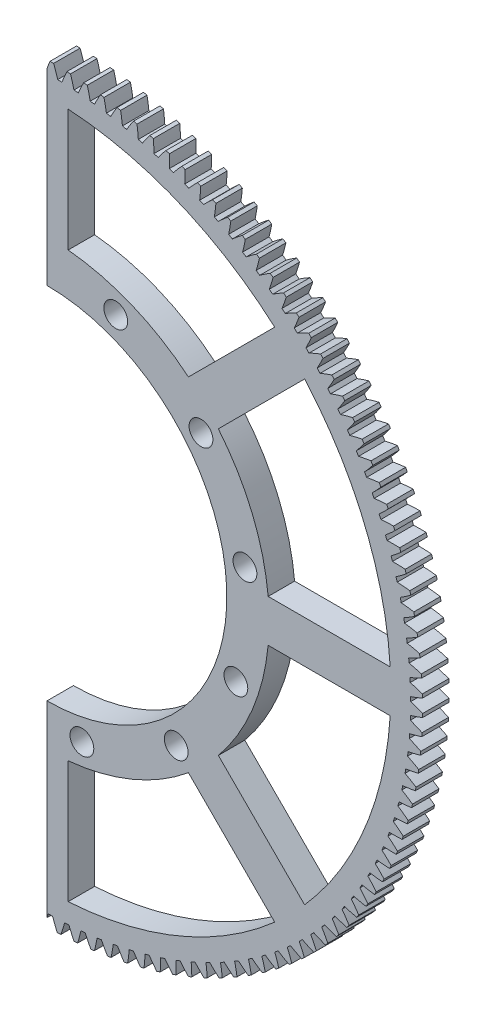
SolidWorks part; units mm, degrees
ref_plane "Front Plane" through (0, 0, 0) normal (0, 0, 1) x (1, 0, 0)
ref_plane "Top Plane" through (0, 0, 0) normal (0, 1, 0) x (1, 0, 0)
ref_plane "Right Plane" through (0, 0, 0) normal (1, 0, 0) x (0, 0, -1)
sketch "Model" plane through (0, 0, 0) normal (0, 0, 1) x (1, 0, 0)
  arc A0 (571.0314, 534.1266) -> (570.3888, 534.6291) centre (528.362, 480.2216) ccw
  arc A1 (573.0789, 535.3705) -> (571.0314, 534.1266) centre (586.5797, 510.8403) ccw
  arc A2 (573.6029, 534.9415) -> (573.0789, 535.3705) centre (528.362, 480.2216) ccw
  arc A3 (572.7875, 532.6888) -> (573.6029, 534.9415) centre (546.891, 543.3365) ccw
  arc A4 (573.4069, 532.158) -> (572.7875, 532.6888) centre (528.362, 480.2216) ccw
  arc A5 (575.5081, 533.3087) -> (573.4069, 532.158) centre (587.8948, 508.1976) ccw
  arc A6 (576.0123, 532.8566) -> (575.5081, 533.3087) centre (528.362, 480.2216) ccw
  arc A7 (575.0967, 530.6428) -> (576.0123, 532.8566) centre (549.704, 542.4416) ccw
  arc A8 (575.6916, 530.0847) -> (575.0967, 530.6428) centre (528.362, 480.2216) ccw
  arc A9 (577.8424, 531.1401) -> (575.6916, 530.0847) centre (589.09, 505.4985) ccw
  arc A10 (578.3258, 530.6658) -> (577.8424, 531.1401) centre (528.362, 480.2216) ccw
  arc A11 (577.3118, 528.4953) -> (578.3258, 530.6658) centre (552.474, 541.4215) ccw
  arc A12 (577.8811, 527.9111) -> (577.3118, 528.4953) centre (528.362, 480.2216) ccw
  arc A13 (580.077, 528.8689) -> (577.8811, 527.9111) centre (590.1629, 502.7485) ccw
  arc A14 (580.5387, 528.3734) -> (580.077, 528.8689) centre (528.362, 480.2216) ccw
  arc A15 (579.4283, 526.2505) -> (580.5387, 528.3734) centre (555.1955, 540.2781) ccw
  arc A16 (579.9708, 525.6414) -> (579.4283, 526.2505) centre (528.362, 480.2216) ccw
  arc A17 (582.2075, 526.4997) -> (579.9708, 525.6414) centre (591.1113, 499.9531) ccw
  arc A18 (582.6465, 525.984) -> (582.2075, 526.4997) centre (528.362, 480.2216) ccw
  arc A19 (581.4419, 523.9131) -> (582.6465, 525.984) centre (557.8629, 539.0137) ccw
  arc A20 (581.9566, 523.2803) -> (581.4419, 523.9131) centre (528.362, 480.2216) ccw
  arc A21 (584.2295, 524.0373) -> (581.9566, 523.2803) centre (591.9334, 497.118) ccw
  arc A22 (584.6449, 523.5025) -> (584.2295, 524.0373) centre (528.362, 480.2216) ccw
  arc A23 (583.3487, 521.4877) -> (584.6449, 523.5025) centre (560.4709, 537.631) ccw
  arc A24 (583.8344, 520.8324) -> (583.3487, 521.4877) centre (528.362, 480.2216) ccw
  arc A25 (586.1391, 521.4867) -> (583.8344, 520.8324) centre (592.6274, 494.2489) ccw
  arc A26 (586.53, 520.9338) -> (586.1391, 521.4867) centre (528.362, 480.2216) ccw
  arc A27 (585.1447, 518.9792) -> (586.53, 520.9338) centre (563.0142, 536.1326) ccw
  arc A28 (585.6006, 518.3027) -> (585.1447, 518.9792) centre (528.362, 480.2216) ccw
  arc A29 (587.9322, 518.853) -> (585.6006, 518.3027) centre (593.192, 491.3515) ccw
  arc A30 (588.298, 518.2831) -> (587.9322, 518.853) centre (528.362, 480.2216) ccw
  arc A31 (586.8264, 516.3926) -> (588.298, 518.2831) centre (565.4877, 534.5216) ccw
  arc A32 (587.2514, 515.6964) -> (586.8264, 516.3926) centre (528.362, 480.2216) ccw
  arc A33 (589.6055, 516.1415) -> (587.2514, 515.6964) centre (593.6261, 488.4317) ccw
  arc A34 (589.9453, 515.5557) -> (589.6055, 516.1415) centre (528.362, 480.2216) ccw
  arc A35 (588.3903, 513.7332) -> (589.9453, 515.5557) centre (567.8865, 532.8013) ccw
  arc A36 (588.7837, 513.0186) -> (588.3903, 513.7332) centre (528.362, 480.2216) ccw
  arc A37 (591.1553, 513.3577) -> (588.7837, 513.0186) centre (593.9287, 485.4954) ccw
  arc A38 (591.4685, 512.7572) -> (591.1553, 513.3577) centre (528.362, 480.2216) ccw
  arc A39 (589.8334, 511.0063) -> (591.4685, 512.7572) centre (570.2057, 530.9751) ccw
  arc A40 (590.1943, 510.2748) -> (589.8334, 511.0063) centre (528.362, 480.2216) ccw
  arc A41 (592.5787, 510.5071) -> (590.1943, 510.2748) centre (594.0993, 482.5484) ccw
  arc A42 (592.8647, 509.8932) -> (592.5787, 510.5071) centre (528.362, 480.2216) ccw
  arc A43 (591.1526, 508.2174) -> (592.8647, 509.8932) centre (572.4406, 529.0467) ccw
  arc A44 (591.4804, 507.4704) -> (591.1526, 508.2174) centre (528.362, 480.2216) ccw
  arc A45 (593.8728, 507.5955) -> (591.4804, 507.4704) centre (594.1375, 479.5968) ccw
  arc A46 (594.1309, 506.9694) -> (593.8728, 507.5955) centre (528.362, 480.2216) ccw
  arc A47 (592.3454, 505.3721) -> (594.1309, 506.9694) centre (574.5867, 527.0199) ccw
  arc A48 (592.6393, 504.6112) -> (592.3454, 505.3721) centre (528.362, 480.2216) ccw
  arc A49 (595.035, 504.6288) -> (592.6393, 504.6112) centre (594.0432, 476.6464) ccw
  arc A50 (595.2648, 503.9918) -> (595.035, 504.6288) centre (528.362, 480.2216) ccw
  arc A51 (593.4094, 502.4762) -> (595.2648, 503.9918) centre (576.6398, 524.899) ccw
  arc A52 (593.6688, 501.7028) -> (593.4094, 502.4762) centre (528.362, 480.2216) ccw
  arc A53 (596.0629, 501.613) -> (593.6688, 501.7028) centre (593.8167, 473.7032) ccw
  arc A54 (596.2638, 500.9662) -> (596.0629, 501.613) centre (528.362, 480.2216) ccw
  arc A55 (594.3423, 499.5354) -> (596.2638, 500.9662) centre (578.5956, 522.688) ccw
  arc A56 (594.5668, 498.7512) -> (594.3423, 499.5354) centre (528.362, 480.2216) ccw
  arc A57 (596.9544, 498.554) -> (594.5668, 498.7512) centre (593.4583, 470.7732) ccw
  arc A58 (597.1262, 497.899) -> (596.9544, 498.554) centre (528.362, 480.2216) ccw
  arc A59 (595.1424, 496.5558) -> (597.1262, 497.899) centre (580.4503, 520.3915) ccw
  arc A60 (595.3315, 495.7623) -> (595.1424, 496.5558) centre (528.362, 480.2216) ccw
  arc A61 (597.7078, 495.4582) -> (595.3315, 495.7623) centre (592.9689, 467.8621) ccw
  arc A62 (597.85, 494.7961) -> (597.7078, 495.4582) centre (528.362, 480.2216) ccw
  arc A63 (595.808, 493.5432) -> (597.85, 494.7961) centre (582.2, 518.0141) ccw
  arc A64 (595.9613, 492.7421) -> (595.808, 493.5432) centre (528.362, 480.2216) ccw
  arc A65 (598.3216, 492.3317) -> (595.9613, 492.7421) centre (592.3493, 464.976) ccw
  arc A66 (598.4339, 491.6638) -> (598.3216, 492.3317) centre (528.362, 480.2216) ccw
  arc A67 (596.3377, 490.5039) -> (598.4339, 491.6638) centre (583.8414, 515.5606) ccw
  arc A68 (596.4549, 489.6966) -> (596.3377, 490.5039) centre (528.362, 480.2216) ccw
  arc A69 (598.7945, 489.1807) -> (596.4549, 489.6966) centre (591.6009, 462.1206) ccw
  arc A70 (598.8767, 488.5085) -> (598.7945, 489.1807) centre (528.362, 480.2216) ccw
  arc A71 (596.7306, 487.4438) -> (598.8767, 488.5085) centre (585.371, 513.036) ccw
  arc A72 (596.8115, 486.6321) -> (596.7306, 487.4438) centre (528.362, 480.2216) ccw
  arc A73 (599.1255, 486.0118) -> (596.8115, 486.6321) centre (590.7251, 459.3016) ccw
  arc A74 (599.1775, 485.3366) -> (599.1255, 486.0118) centre (528.362, 480.2216) ccw
  arc A75 (596.9858, 484.3692) -> (599.1775, 485.3366) centre (586.7858, 510.4452) ccw
  arc A76 (597.0301, 483.5547) -> (596.9858, 484.3692) centre (528.362, 480.2216) ccw
  arc A77 (599.314, 482.8312) -> (597.0301, 483.5547) centre (589.7237, 456.5248) ccw
  arc A78 (599.3357, 482.1543) -> (599.314, 482.8312) centre (528.362, 480.2216) ccw
  arc A79 (597.1027, 481.2862) -> (599.3357, 482.1543) centre (588.083, 507.7936) ccw
  arc A80 (597.1105, 480.4705) -> (597.1027, 481.2862) centre (528.362, 480.2216) ccw
  arc A81 (599.3596, 479.6453) -> (597.1105, 480.4705) centre (588.5988, 453.7956) ccw
  arc A82 (599.3509, 478.9681) -> (599.3596, 479.6453) centre (528.362, 480.2216) ccw
  arc A83 (597.0813, 478.2011) -> (599.3509, 478.9681) centre (589.2598, 505.0865) ccw
  arc A84 (597.0525, 477.3859) -> (597.0813, 478.2011) centre (528.362, 480.2216) ccw
  arc A85 (599.2623, 476.4606) -> (597.0525, 477.3859) centre (587.3525, 451.1197) ccw
  arc A86 (599.2232, 475.7845) -> (599.2623, 476.4606) centre (528.362, 480.2216) ccw
  arc A87 (596.9214, 475.12) -> (599.2232, 475.7845) centre (590.3141, 502.3293) ccw
  arc A88 (596.8561, 474.307) -> (596.9214, 475.12) centre (528.362, 480.2216) ccw
  arc A89 (599.0222, 473.2834) -> (596.8561, 474.307) centre (585.9875, 448.5024) ccw
  arc A90 (598.9528, 472.6098) -> (599.0222, 473.2834) centre (528.362, 480.2216) ccw
  arc A91 (596.6235, 472.0493) -> (598.9528, 472.6098) centre (591.2435, 499.5276) ccw
  arc A92 (596.5217, 471.2399) -> (596.6235, 472.0493) centre (528.362, 480.2216) ccw
  arc A93 (598.6397, 470.1202) -> (596.5217, 471.2399) centre (584.5064, 445.949) ccw
  arc A94 (598.5402, 469.4504) -> (598.6397, 470.1202) centre (528.362, 480.2216) ccw
  arc A95 (596.1881, 468.995) -> (598.5402, 469.4504) centre (592.0464, 496.6869) ccw
  arc A96 (596.0502, 468.191) -> (596.1881, 468.995) centre (528.362, 480.2216) ccw
  arc A97 (598.1158, 466.9774) -> (596.0502, 468.191) centre (582.9122, 443.4646) ccw
  arc A98 (597.9863, 466.3127) -> (598.1158, 466.9774) centre (528.362, 480.2216) ccw
  arc A99 (595.6161, 465.9633) -> (597.9863, 466.3127) centre (592.721, 493.8132) ccw
  arc A100 (595.4422, 465.1663) -> (595.6161, 465.9633) centre (528.362, 480.2216) ccw
  arc A101 (597.4513, 463.8613) -> (595.4422, 465.1663) centre (581.2082, 441.0542) ccw
  arc A102 (597.2921, 463.203) -> (597.4513, 463.8613) centre (528.362, 480.2216) ccw
  arc A103 (594.9087, 462.9603) -> (597.2921, 463.203) centre (593.2659, 490.912) ccw
  arc A104 (594.6992, 462.1719) -> (594.9087, 462.9603) centre (528.362, 480.2216) ccw
  arc A105 (596.6478, 460.7781) -> (594.6992, 462.1719) centre (579.3977, 438.7227) ccw
  arc A106 (596.4592, 460.1276) -> (596.6478, 460.7781) centre (528.362, 480.2216) ccw
  arc A107 (594.0673, 459.992) -> (596.4592, 460.1276) centre (593.6802, 487.9894) ccw
  arc A108 (593.8226, 459.2139) -> (594.0673, 459.992) centre (528.362, 480.2216) ccw
  arc A109 (595.7067, 457.734) -> (593.8226, 459.2139) centre (577.4845, 436.4748) ccw
  arc A110 (595.4891, 457.0927) -> (595.7067, 457.734) centre (528.362, 480.2216) ccw
  arc A111 (593.0935, 457.0646) -> (595.4891, 457.0927) centre (593.9629, 485.0511) ccw
  arc A112 (592.8142, 456.2982) -> (593.0935, 457.0646) centre (528.362, 480.2216) ccw
  arc A113 (594.6299, 454.7352) -> (592.8142, 456.2982) centre (575.4724, 434.315) ccw
  arc A114 (594.3838, 454.1043) -> (594.6299, 454.7352) centre (528.362, 480.2216) ccw
  arc A115 (591.9894, 454.1837) -> (594.3838, 454.1043) centre (594.1136, 482.103) ccw
  arc A116 (591.676, 453.4306) -> (591.9894, 454.1837) centre (528.362, 480.2216) ccw
  arc A117 (593.4198, 451.7878) -> (591.676, 453.4306) centre (573.3653, 432.2476) ccw
  arc A118 (593.1456, 451.1686) -> (593.4198, 451.7878) centre (528.362, 480.2216) ccw
  arc A119 (590.7572, 451.3553) -> (593.1456, 451.1686) centre (594.1318, 479.1512) ccw
  arc A120 (590.4103, 450.617) -> (590.7572, 451.3553) centre (528.362, 480.2216) ccw
  arc A121 (592.0786, 448.8976) -> (590.4103, 450.617) centre (571.1677, 430.2769) ccw
  arc A122 (591.7769, 448.2913) -> (592.0786, 448.8976) centre (528.362, 480.2216) ccw
  arc A123 (589.3992, 448.585) -> (591.7769, 448.2913) centre (594.0175, 476.2015) ccw
  arc A124 (589.0196, 447.863) -> (589.3992, 448.585) centre (528.362, 480.2216) ccw
  arc A125 (590.6091, 446.0705) -> (589.0196, 447.863) centre (568.8838, 428.4067) ccw
  arc A126 (590.2805, 445.4784) -> (590.6091, 446.0705) centre (528.362, 480.2216) ccw
  arc A127 (587.9184, 445.8784) -> (590.2805, 445.4784) centre (593.771, 473.2599) ccw
  arc A128 (587.5067, 445.1742) -> (587.9184, 445.8784) centre (528.362, 480.2216) ccw
  arc A129 (589.0142, 443.3122) -> (587.5067, 445.1742) centre (566.5183, 426.6408) ccw
  arc A130 (588.6594, 442.7354) -> (589.0142, 443.3122) centre (528.362, 480.2216) ccw
  arc A131 (586.3176, 443.241) -> (588.6594, 442.7354) centre (593.3928, 470.3324) ccw
  arc A132 (585.8748, 442.556) -> (586.3176, 443.241) centre (528.362, 480.2216) ccw
  arc A133 (587.2972, 440.6282) -> (585.8748, 442.556) centre (564.076, 424.9829) ccw
  arc A134 (586.9169, 440.0679) -> (587.2972, 440.6282) centre (528.362, 480.2216) ccw
  arc A135 (584.6002, 440.6781) -> (586.9169, 440.0679) centre (592.8837, 467.4247) ccw
  arc A136 (584.127, 440.0136) -> (584.6002, 440.6781) centre (528.362, 480.2216) ccw
  arc A137 (585.4615, 438.024) -> (584.127, 440.0136) centre (561.5618, 423.4362) ccw
  arc A138 (585.0564, 437.4813) -> (585.4615, 438.024) centre (528.362, 480.2216) ccw
  arc A139 (582.7694, 438.1948) -> (585.0564, 437.4813) centre (592.2446, 464.5429) ccw
  arc A140 (582.2669, 437.5522) -> (582.7694, 438.1948) centre (528.362, 480.2216) ccw
  arc A141 (583.5108, 435.5047) -> (582.2669, 437.5522) centre (558.9807, 422.0039) ccw
  arc A142 (583.0818, 434.9807) -> (583.5108, 435.5047) centre (528.362, 480.2216) ccw
  arc A143 (580.8291, 435.7961) -> (583.0818, 434.9807) centre (591.4768, 461.6926) ccw
  arc A144 (580.2983, 435.1767) -> (580.8291, 435.7961) centre (528.362, 480.2216) ccw
  arc A145 (581.4491, 433.0755) -> (580.2983, 435.1767) centre (556.3379, 420.6888) ccw
  arc A146 (580.997, 432.5713) -> (581.4491, 433.0755) centre (528.362, 480.2216) ccw
  arc A147 (578.7831, 433.4869) -> (580.997, 432.5713) centre (590.582, 458.8796) ccw
  arc A148 (578.2251, 432.892) -> (578.7831, 433.4869) centre (528.362, 480.2216) ccw
  arc A149 (579.2804, 430.7412) -> (578.2251, 432.892) centre (553.6388, 419.4936) ccw
  arc A150 (578.8061, 430.2578) -> (579.2804, 430.7412) centre (528.362, 480.2216) ccw
  arc A151 (576.6356, 431.2719) -> (578.8061, 430.2578) centre (589.5618, 456.1096) ccw
  arc A152 (576.0514, 430.7025) -> (576.6356, 431.2719) centre (528.362, 480.2216) ccw
  arc A153 (577.0092, 428.5066) -> (576.0514, 430.7025) centre (550.8888, 418.4207) ccw
  arc A154 (576.5137, 428.0449) -> (577.0092, 428.5066) centre (528.362, 480.2216) ccw
  arc A155 (574.3909, 429.1554) -> (576.5137, 428.0449) centre (588.4184, 453.3882) ccw
  arc A156 (573.7817, 428.6128) -> (574.3909, 429.1554) centre (528.362, 480.2216) ccw
  arc A157 (574.64, 426.3761) -> (573.7817, 428.6128) centre (548.0934, 417.4723) ccw
  arc A158 (574.1243, 425.9372) -> (574.64, 426.3761) centre (528.362, 480.2216) ccw
  arc A159 (572.0534, 427.1417) -> (574.1243, 425.9372) centre (587.154, 450.7208) ccw
  arc A160 (571.4206, 426.627) -> (572.0534, 427.1417) centre (528.362, 480.2216) ccw
  arc A161 (572.1777, 424.3541) -> (571.4206, 426.627) centre (545.2583, 416.6503) ccw
  arc A162 (571.6428, 423.9387) -> (572.1777, 424.3541) centre (528.362, 480.2216) ccw
  arc A163 (569.628, 425.2349) -> (571.6428, 423.9387) centre (585.7713, 448.1128) ccw
  arc A164 (568.9727, 424.7492) -> (569.628, 425.2349) centre (528.362, 480.2216) ccw
  arc A165 (569.6271, 422.4446) -> (568.9727, 424.7492) centre (542.3892, 415.9562) ccw
  arc A166 (569.0741, 422.0536) -> (569.6271, 422.4446) centre (528.362, 480.2216) ccw
  arc A167 (567.1195, 423.4389) -> (569.0741, 422.0536) centre (584.2729, 445.5694) ccw
  arc A168 (566.4431, 422.9831) -> (567.1195, 423.4389) centre (528.362, 480.2216) ccw
  arc A169 (566.9934, 420.6514) -> (566.4431, 422.9831) centre (539.4918, 415.3916) ccw
  arc A170 (566.4234, 420.2856) -> (566.9934, 420.6514) centre (528.362, 480.2216) ccw
  arc A171 (564.5329, 421.7572) -> (566.4234, 420.2856) centre (582.662, 443.0959) ccw
  arc A172 (563.8367, 421.3322) -> (564.5329, 421.7572) centre (528.362, 480.2216) ccw
  arc A173 (564.2818, 418.9782) -> (563.8367, 421.3322) centre (536.572, 414.9575) ccw
  arc A174 (563.6961, 418.6383) -> (564.2818, 418.9782) centre (528.362, 480.2216) ccw
  arc A175 (561.8735, 420.1933) -> (563.6961, 418.6383) centre (580.9416, 440.6971) ccw
  arc A176 (561.1589, 419.7999) -> (561.8735, 420.1933) centre (528.362, 480.2216) ccw
  arc A177 (561.498, 417.4283) -> (561.1589, 419.7999) centre (533.6357, 414.6549) ccw
  arc A178 (560.8976, 417.1151) -> (561.498, 417.4283) centre (528.362, 480.2216) ccw
  arc A179 (559.1466, 418.7503) -> (560.8976, 417.1151) centre (579.1154, 438.3779) ccw
  arc A180 (558.4151, 418.3893) -> (559.1466, 418.7503) centre (528.362, 480.2216) ccw
  arc A181 (558.6474, 416.0049) -> (558.4151, 418.3893) centre (530.6887, 414.4843) ccw
  arc A182 (558.0335, 415.7189) -> (558.6474, 416.0049) centre (528.362, 480.2216) ccw
  arc A183 (556.3577, 417.431) -> (558.0335, 415.7189) centre (577.187, 436.143) ccw
  arc A184 (555.6107, 417.1033) -> (556.3577, 417.431) centre (528.362, 480.2216) ccw
  arc A185 (555.7359, 414.7108) -> (555.6107, 417.1033) centre (527.7371, 414.4461) ccw
  arc A186 (555.1097, 414.4527) -> (555.7359, 414.7108) centre (528.362, 480.2216) ccw
  arc A187 (553.5124, 416.2382) -> (555.1097, 414.4527) centre (575.1603, 433.9969) ccw
  arc A188 (552.7515, 415.9443) -> (553.5124, 416.2382) centre (528.362, 480.2216) ccw
  arc A189 (552.7692, 413.5486) -> (552.7515, 415.9443) centre (524.7867, 414.5404) ccw
  arc A190 (552.1321, 413.3189) -> (552.7692, 413.5486) centre (528.362, 480.2216) ccw
  arc A191 (550.6165, 415.1743) -> (552.1321, 413.3189) centre (573.0393, 431.9438) ccw
  arc A192 (549.8432, 414.9148) -> (550.6165, 415.1743) centre (528.362, 480.2216) ccw
  arc A193 (549.7533, 412.5208) -> (549.8432, 414.9148) centre (521.8435, 414.7669) ccw
  arc A194 (549.1066, 412.3198) -> (549.7533, 412.5208) centre (528.362, 480.2216) ccw
  arc A195 (547.6758, 414.2413) -> (549.1066, 412.3198) centre (570.8283, 429.988) ccw
  arc A196 (546.8915, 414.0168) -> (547.6758, 414.2413) centre (528.362, 480.2216) ccw
  arc A197 (546.6944, 411.6292) -> (546.8915, 414.0168) centre (518.9135, 415.1253) ccw
  arc A198 (546.0393, 411.4575) -> (546.6944, 411.6292) centre (528.362, 480.2216) ccw
  arc A199 (544.6961, 413.4412) -> (546.0393, 411.4575) centre (568.5318, 428.1333) ccw
  arc A200 (543.9026, 413.2521) -> (544.6961, 413.4412) centre (528.362, 480.2216) ccw
  arc A201 (543.5985, 410.8758) -> (543.9026, 413.2521) centre (516.0025, 415.6147) ccw
  arc A202 (542.9364, 410.7336) -> (543.5985, 410.8758) centre (528.362, 480.2216) ccw
  arc A203 (541.6836, 412.7757) -> (542.9364, 410.7336) centre (566.1545, 426.3836) ccw
  arc A204 (540.8824, 412.6224) -> (541.6836, 412.7757) centre (528.362, 480.2216) ccw
  arc A205 (540.472, 410.262) -> (540.8824, 412.6224) centre (513.1163, 416.2343) ccw
  arc A206 (539.8042, 410.1497) -> (540.472, 410.262) centre (528.362, 480.2216) ccw
  arc A207 (538.6442, 412.2459) -> (539.8042, 410.1497) centre (563.701, 424.7422) ccw
  arc A208 (537.837, 412.1287) -> (538.6442, 412.2459) centre (528.362, 480.2216) ccw
  arc A209 (537.3211, 409.7892) -> (537.837, 412.1287) centre (510.2609, 416.9827) ccw
  arc A210 (536.6489, 409.7069) -> (537.3211, 409.7892) centre (528.362, 480.2216) ccw
  arc A211 (535.5841, 411.853) -> (536.6489, 409.7069) centre (561.1763, 423.2126) ccw
  arc A212 (534.7724, 411.7722) -> (535.5841, 411.853) centre (528.362, 480.2216) ccw
  arc A213 (534.1521, 409.4581) -> (534.7724, 411.7722) centre (507.4419, 417.8585) ccw
  arc A214 (533.4769, 409.4061) -> (534.1521, 409.4581) centre (528.362, 480.2216) ccw
  arc A215 (532.5095, 411.5979) -> (533.4769, 409.4061) centre (558.5856, 421.7978) ccw
  arc A216 (531.695, 411.5535) -> (532.5095, 411.5979) centre (528.362, 480.2216) ccw
  arc A217 (530.9715, 409.2696) -> (531.695, 411.5535) centre (504.6651, 418.8599) ccw
  arc A218 (530.2946, 409.248) -> (530.9715, 409.2696) centre (528.362, 480.2216) ccw
  arc A219 (529.4265, 411.4809) -> (530.2946, 409.248) centre (555.934, 420.5007) ccw
  arc A220 (528.6109, 411.4731) -> (529.4265, 411.4809) centre (528.362, 480.2216) ccw
  arc A221 (527.7856, 409.224) -> (528.6109, 411.4731) centre (501.936, 419.9848) ccw
  arc A222 (527.1084, 409.2327) -> (527.7856, 409.224) centre (528.362, 480.2216) ccw
  arc A223 (526.3414, 411.5023) -> (527.1084, 409.2327) centre (553.2268, 419.3238) ccw
  arc A224 (525.5262, 411.5312) -> (526.3414, 411.5023) centre (528.362, 480.2216) ccw
  arc A225 (524.6009, 409.3213) -> (525.5262, 411.5312) centre (499.2601, 421.2311) ccw
  arc A226 (523.9248, 409.3604) -> (524.6009, 409.3213) centre (528.362, 480.2216) ccw
  arc A227 (523.2604, 411.6622) -> (523.9248, 409.3604) centre (550.4696, 418.2696) ccw
  arc A228 (522.4473, 411.7275) -> (523.2604, 411.6622) centre (528.362, 480.2216) ccw
  arc A229 (521.4238, 409.5615) -> (522.4473, 411.7275) centre (496.6428, 422.5961) ccw
  arc A230 (520.7501, 409.6309) -> (521.4238, 409.5615) centre (528.362, 480.2216) ccw
  arc A231 (520.1896, 411.9601) -> (520.7501, 409.6309) centre (547.6679, 417.3401) ccw
  arc A232 (519.3803, 412.0619) -> (520.1896, 411.9601) centre (528.362, 480.2216) ccw
  arc A233 (518.2606, 409.9439) -> (519.3803, 412.0619) centre (494.0893, 424.0772) ccw
  arc A234 (517.5907, 410.0434) -> (518.2606, 409.9439) centre (528.362, 480.2216) ccw
  arc A235 (517.1353, 412.3955) -> (517.5907, 410.0434) centre (544.8273, 416.5372) ccw
  arc A236 (516.3313, 412.5335) -> (517.1353, 412.3955) centre (528.362, 480.2216) ccw
  arc A237 (515.1178, 410.4679) -> (516.3313, 412.5335) centre (491.6049, 425.6714) ccw
  arc A238 (514.453, 410.5974) -> (515.1178, 410.4679) centre (528.362, 480.2216) ccw
  arc A239 (514.1036, 412.9675) -> (514.453, 410.5974) centre (541.9535, 415.8627) ccw
  arc A240 (513.3066, 413.1414) -> (514.1036, 412.9675) centre (528.362, 480.2216) ccw
  arc A241 (512.0016, 411.1323) -> (513.3066, 413.1414) centre (489.1946, 427.3754) ccw
  arc A242 (511.3433, 411.2915) -> (512.0016, 411.1323) centre (528.362, 480.2216) ccw
  arc A243 (511.1006, 413.6749) -> (511.3433, 411.2915) centre (539.0524, 415.3177) ccw
  arc A244 (510.3123, 413.8844) -> (511.1006, 413.6749) centre (528.362, 480.2216) ccw
  arc A245 (508.9184, 411.9359) -> (510.3123, 413.8844) centre (486.8631, 429.1859) ccw
  arc A246 (508.2679, 412.1244) -> (508.9184, 411.9359) centre (528.362, 480.2216) ccw
  arc A247 (508.1324, 414.5163) -> (508.2679, 412.1244) centre (536.1297, 414.9034) ccw
  arc A248 (507.3542, 414.761) -> (508.1324, 414.5163) centre (528.362, 480.2216) ccw
  arc A249 (505.8743, 412.877) -> (507.3542, 414.761) centre (484.6151, 431.0991) ccw
  arc A250 (505.233, 413.0945) -> (505.8743, 412.877) centre (528.362, 480.2216) ccw
  arc A251 (505.2049, 415.4901) -> (505.233, 413.0945) centre (533.1914, 414.6207) ccw
  arc A252 (504.4385, 415.7694) -> (505.2049, 415.4901) centre (528.362, 480.2216) ccw
  arc A253 (502.8756, 413.9537) -> (504.4385, 415.7694) centre (482.4553, 433.1113) ccw
  arc A254 (502.2447, 414.1998) -> (502.8756, 413.9537) centre (528.362, 480.2216) ccw
  arc A255 (502.324, 416.5942) -> (502.2447, 414.1998) centre (530.2433, 414.4701) ccw
  arc A256 (501.5709, 416.9076) -> (502.324, 416.5942) centre (528.362, 480.2216) ccw
  arc A257 (499.9281, 415.1639) -> (501.5709, 416.9076) centre (480.3879, 435.2183) ccw
  arc A258 (499.3089, 415.438) -> (499.9281, 415.1639) centre (528.362, 480.2216) ccw
  arc A259 (499.4956, 417.8265) -> (499.3089, 415.438) centre (527.2915, 414.4519) ccw
  arc A260 (498.7573, 418.1734) -> (499.4956, 417.8265) centre (528.362, 480.2216) ccw
  arc A261 (497.038, 416.505) -> (498.7573, 418.1734) centre (478.4172, 437.416) ccw
  arc A262 (496.4316, 416.8067) -> (497.038, 416.505) centre (528.362, 480.2216) ccw
  arc A263 (496.7253, 419.1844) -> (496.4316, 416.8067) centre (524.3418, 414.5661) ccw
  arc A264 (496.0034, 419.564) -> (496.7253, 419.1844) centre (528.362, 480.2216) ccw
  arc A265 (494.2109, 417.9745) -> (496.0034, 419.564) centre (476.547, 439.6998) ccw
  arc A266 (493.6187, 418.3031) -> (494.2109, 417.9745) centre (528.362, 480.2216) ccw
  arc A267 (494.0188, 420.6652) -> (493.6187, 418.3031) centre (521.4003, 414.8126) ccw
  arc A268 (493.3146, 421.0769) -> (494.0188, 420.6652) centre (528.362, 480.2216) ccw
  arc A269 (491.4526, 419.5694) -> (493.3146, 421.0769) centre (474.7812, 442.0653) ccw
  arc A270 (490.8757, 419.9242) -> (491.4526, 419.5694) centre (528.362, 480.2216) ccw
  arc A271 (491.3814, 422.266) -> (490.8757, 419.9242) centre (518.4727, 415.1908) ccw
  arc A272 (490.6963, 422.7088) -> (491.3814, 422.266) centre (528.362, 480.2216) ccw
  arc A273 (488.7686, 421.2864) -> (490.6963, 422.7088) centre (473.1233, 444.5076) ccw
  arc A274 (488.2082, 421.6667) -> (488.7686, 421.2864) centre (528.362, 480.2216) ccw
  arc A275 (488.8184, 423.9835) -> (488.2082, 421.6667) centre (515.5651, 415.7) ccw
  arc A276 (488.154, 424.4566) -> (488.8184, 423.9835) centre (528.362, 480.2216) ccw
  arc A277 (486.1643, 423.1221) -> (488.154, 424.4566) centre (471.5766, 447.0219) ccw
  arc A278 (485.6216, 423.5272) -> (486.1643, 423.1221) centre (528.362, 480.2216) ccw
  arc A279 (486.3351, 425.8142) -> (485.6216, 423.5272) centre (512.6832, 416.3391) ccw
  arc A280 (485.6925, 426.3167) -> (486.3351, 425.8142) centre (528.362, 480.2216) ccw
  arc A281 (483.645, 425.0728) -> (485.6925, 426.3167) centre (470.1442, 449.603) ccw
  arc A282 (483.121, 425.5018) -> (483.645, 425.0728) centre (528.362, 480.2216) ccw
  arc A283 (483.9365, 427.7545) -> (483.121, 425.5018) centre (509.8329, 417.1068) ccw
  arc A284 (483.3171, 428.2853) -> (483.9365, 427.7545) centre (528.362, 480.2216) ccw
  arc A285 (481.2158, 427.1345) -> (483.3171, 428.2853) centre (468.8292, 452.2457) ccw
  arc A286 (480.7116, 427.5867) -> (481.2158, 427.1345) centre (528.362, 480.2216) ccw
  arc A287 (481.6273, 429.8005) -> (480.7116, 427.5867) centre (507.0199, 418.0017) ccw
  arc A288 (481.0323, 430.3585) -> (481.6273, 429.8005) centre (528.362, 480.2216) ccw
  arc A289 (478.8816, 429.3032) -> (481.0323, 430.3585) centre (467.634, 454.9448) ccw
  arc A290 (478.3981, 429.7775) -> (478.8816, 429.3032) centre (528.362, 480.2216) ccw
  arc A291 (479.4122, 431.948) -> (478.3981, 429.7775) centre (504.2499, 419.0218) ccw
  arc A292 (478.8429, 432.5322) -> (479.4122, 431.948) centre (528.362, 480.2216) ccw
  arc A293 (476.6469, 431.5744) -> (478.8429, 432.5322) centre (466.5611, 457.6948) ccw
  arc A294 (476.1853, 432.0699) -> (476.6469, 431.5744) centre (528.362, 480.2216) ccw
  arc A295 (477.2957, 434.1927) -> (476.1853, 432.0699) centre (501.5285, 420.1652) ccw
  arc A296 (476.7532, 434.8019) -> (477.2957, 434.1927) centre (528.362, 480.2216) ccw
  arc A297 (474.5165, 433.9436) -> (476.7532, 434.8019) centre (465.6126, 460.4902) ccw
  arc A298 (474.0775, 434.4593) -> (474.5165, 433.9436) centre (528.362, 480.2216) ccw
  arc A299 (475.282, 436.5302) -> (474.0775, 434.4593) centre (498.8611, 421.4296) ccw
  arc A300 (474.7674, 437.163) -> (475.282, 436.5302) centre (528.362, 480.2216) ccw
  arc A301 (472.4944, 436.4059) -> (474.7674, 437.163) centre (464.7906, 463.3253) ccw
  arc A302 (472.079, 436.9408) -> (472.4944, 436.4059) centre (528.362, 480.2216) ccw
  arc A303 (473.3753, 438.9556) -> (472.079, 436.9408) centre (496.2531, 422.8123) ccw
  arc A304 (472.8895, 439.6109) -> (473.3753, 438.9556) centre (528.362, 480.2216) ccw
  arc A305 (470.5849, 438.9566) -> (472.8895, 439.6109) centre (464.0965, 466.1944) ccw
  arc A306 (470.1939, 439.5095) -> (470.5849, 438.9566) centre (528.362, 480.2216) ccw
  arc A307 (471.5792, 441.4641) -> (470.1939, 439.5095) centre (493.7098, 424.3107) ccw
  arc A308 (471.1234, 442.1406) -> (471.5792, 441.4641) centre (528.362, 480.2216) ccw
  arc A309 (468.7917, 441.5903) -> (471.1234, 442.1406) centre (463.5319, 469.0918) ccw
  arc A310 (468.4259, 442.1602) -> (468.7917, 441.5903) centre (528.362, 480.2216) ccw
  arc A311 (469.8976, 444.0507) -> (468.4259, 442.1602) centre (491.2362, 425.9217) ccw
  arc A312 (469.4725, 444.7469) -> (469.8976, 444.0507) centre (528.362, 480.2216) ccw
  arc A313 (467.1185, 444.3018) -> (469.4725, 444.7469) centre (463.0979, 472.0116) ccw
  arc A314 (466.7787, 444.8876) -> (467.1185, 444.3018) centre (528.362, 480.2216) ccw
  arc A315 (468.3336, 446.7101) -> (466.7787, 444.8876) centre (488.8375, 427.642) ccw
  arc A316 (467.9403, 447.4247) -> (468.3336, 446.7101) centre (528.362, 480.2216) ccw
  arc A317 (465.5686, 447.0856) -> (467.9403, 447.4247) centre (462.7952, 474.9479) ccw
  arc A318 (465.2554, 447.6861) -> (465.5686, 447.0856) centre (528.362, 480.2216) ccw
  arc A319 (466.8906, 449.437) -> (465.2554, 447.6861) centre (486.5183, 429.4682) ccw
  arc A320 (466.5297, 450.1685) -> (466.8906, 449.437) centre (528.362, 480.2216) ccw
  arc A321 (464.1452, 449.9362) -> (466.5297, 450.1685) centre (462.6247, 477.8949) ccw
  arc A322 (463.8593, 450.5501) -> (464.1452, 449.9362) centre (528.362, 480.2216) ccw
  arc A323 (465.5713, 452.2259) -> (463.8593, 450.5501) centre (484.2834, 431.3966) ccw
  arc A324 (465.2436, 452.9729) -> (465.5713, 452.2259) centre (528.362, 480.2216) ccw
  arc A325 (462.8511, 452.8478) -> (465.2436, 452.9729) centre (462.5865, 480.8465) ccw
  arc A326 (462.593, 453.4739) -> (462.8511, 452.8478) centre (528.362, 480.2216) ccw
  arc A327 (464.3785, 455.0712) -> (462.593, 453.4739) centre (482.1372, 433.4233) ccw
  arc A328 (464.0846, 455.8321) -> (464.3785, 455.0712) centre (528.362, 480.2216) ccw
  arc A329 (461.689, 455.8145) -> (464.0846, 455.8321) centre (462.6807, 483.7969) ccw
  arc A330 (461.4592, 456.4515) -> (461.689, 455.8145) centre (528.362, 480.2216) ccw
  arc A331 (463.3146, 457.9671) -> (461.4592, 456.4515) centre (480.0842, 435.5443) ccw
  arc A332 (463.0551, 458.7405) -> (463.3146, 457.9671) centre (528.362, 480.2216) ccw
  arc A333 (460.6611, 458.8303) -> (463.0551, 458.7405) centre (462.9073, 486.7401) ccw
  arc A334 (460.4601, 459.477) -> (460.6611, 458.8303) centre (528.362, 480.2216) ccw
  arc A335 (462.3817, 460.9079) -> (460.4601, 459.477) centre (478.1283, 437.7553) ccw
  arc A336 (462.1571, 461.6921) -> (462.3817, 460.9079) centre (528.362, 480.2216) ccw
  arc A337 (459.7695, 461.8892) -> (462.1571, 461.6921) centre (463.2656, 489.6701) ccw
  arc A338 (459.5978, 462.5443) -> (459.7695, 461.8892) centre (528.362, 480.2216) ccw
  arc A339 (461.5816, 463.8875) -> (459.5978, 462.5443) centre (476.2737, 440.0518) ccw
  arc A340 (461.3925, 464.681) -> (461.5816, 463.8875) centre (528.362, 480.2216) ccw
  arc A341 (459.0161, 464.9851) -> (461.3925, 464.681) centre (463.7551, 492.5812) ccw
  arc A342 (458.8739, 465.6472) -> (459.0161, 464.9851) centre (528.362, 480.2216) ccw
  arc A343 (460.916, 466.9001) -> (458.8739, 465.6472) centre (474.5239, 442.4292) ccw
  arc A344 (460.7627, 467.7012) -> (460.916, 466.9001) centre (528.362, 480.2216) ccw
  arc A345 (458.4024, 468.1116) -> (460.7627, 467.7012) centre (464.3746, 495.4673) ccw
  arc A346 (458.29, 468.7795) -> (458.4024, 468.1116) centre (528.362, 480.2216) ccw
  arc A347 (460.3862, 469.9394) -> (458.29, 468.7795) centre (472.8826, 444.8827) ccw
  arc A348 (460.269, 470.7467) -> (460.3862, 469.9394) centre (528.362, 480.2216) ccw
  arc A349 (457.9295, 471.2625) -> (460.269, 470.7467) centre (465.1231, 498.3227) ccw
  arc A350 (457.8472, 471.9348) -> (457.9295, 471.2625) centre (528.362, 480.2216) ccw
  arc A351 (459.9934, 472.9995) -> (457.8472, 471.9348) centre (471.353, 447.4073) ccw
  arc A352 (459.9125, 473.8112) -> (459.9934, 472.9995) centre (528.362, 480.2216) ccw
  arc A353 (457.5985, 474.4315) -> (459.9125, 473.8112) centre (465.9988, 501.1417) ccw
  arc A354 (457.5465, 475.1067) -> (457.5985, 474.4315) centre (528.362, 480.2216) ccw
  arc A355 (459.7382, 476.0741) -> (457.5465, 475.1067) centre (469.9382, 449.9981) ccw
  arc A356 (459.6938, 476.8886) -> (459.7382, 476.0741) centre (528.362, 480.2216) ccw
  arc A357 (457.41, 477.6121) -> (459.6938, 476.8886) centre (467.0002, 503.9185) ccw
  arc A358 (457.3883, 478.289) -> (457.41, 477.6121) centre (528.362, 480.2216) ccw
  arc A359 (459.6212, 479.1571) -> (457.3883, 478.289) centre (468.641, 452.6497) ccw
  arc A360 (459.6134, 479.9728) -> (459.6212, 479.1571) centre (528.362, 480.2216) ccw
  arc A361 (457.3643, 480.798) -> (459.6134, 479.9728) centre (468.1252, 506.6477) ccw
  arc A362 (457.373, 481.4752) -> (457.3643, 480.798) centre (528.362, 480.2216) ccw
  arc A363 (459.6427, 482.2422) -> (457.373, 481.4752) centre (467.4641, 455.3568) ccw
  arc A364 (459.6715, 483.0574) -> (459.6427, 482.2422) centre (528.362, 480.2216) ccw
  arc A365 (457.4617, 483.9827) -> (459.6715, 483.0574) centre (469.3714, 509.3236) ccw
  arc A366 (457.5008, 484.6588) -> (457.4617, 483.9827) centre (528.362, 480.2216) ccw
  arc A367 (459.8025, 485.3232) -> (457.5008, 484.6588) centre (466.4099, 458.114) ccw
  arc A368 (459.8679, 486.1363) -> (459.8025, 485.3232) centre (528.362, 480.2216) ccw
  arc A369 (457.7018, 487.1599) -> (459.8679, 486.1363) centre (470.7365, 511.9409) ccw
  arc A370 (457.7712, 487.8335) -> (457.7018, 487.1599) centre (528.362, 480.2216) ccw
  arc A371 (460.1004, 488.394) -> (457.7712, 487.8335) centre (465.4804, 460.9157) ccw
  arc A372 (460.2022, 489.2034) -> (460.1004, 488.394) centre (528.362, 480.2216) ccw
  arc A373 (458.0842, 490.323) -> (460.2022, 489.2034) centre (472.2176, 514.4943) ccw
  arc A374 (458.1838, 490.9929) -> (458.0842, 490.323) centre (528.362, 480.2216) ccw
  arc A375 (460.5358, 491.4483) -> (458.1838, 490.9929) centre (464.6776, 463.7563) ccw
  arc A376 (460.6738, 492.2523) -> (460.5358, 491.4483) centre (528.362, 480.2216) ccw
  arc A377 (458.6082, 493.4659) -> (460.6738, 492.2523) centre (473.8117, 516.9787) ccw
  arc A378 (458.7377, 494.1306) -> (458.6082, 493.4659) centre (528.362, 480.2216) ccw
  arc A379 (461.1078, 494.48) -> (458.7377, 494.1306) centre (464.003, 466.6301) ccw
  arc A380 (461.2817, 495.277) -> (461.1078, 494.48) centre (528.362, 480.2216) ccw
  arc A381 (459.2726, 496.582) -> (461.2817, 495.277) centre (475.5158, 519.3891) ccw
  arc A382 (459.4318, 497.2403) -> (459.2726, 496.582) centre (528.362, 480.2216) ccw
  arc A383 (461.8152, 497.483) -> (459.4318, 497.2403) centre (463.458, 469.5313) ccw
  arc A384 (462.0247, 498.2714) -> (461.8152, 497.483) centre (528.362, 480.2216) ccw
  arc A385 (460.0762, 499.6652) -> (462.0247, 498.2714) centre (477.3262, 521.7206) ccw
  arc A386 (460.2648, 500.3157) -> (460.0762, 499.6652) centre (528.362, 480.2216) ccw
  arc A387 (462.6567, 500.4513) -> (460.2648, 500.3157) centre (463.0437, 472.4539) ccw
  arc A388 (462.9013, 501.2294) -> (462.6567, 500.4513) centre (528.362, 480.2216) ccw
  arc A389 (461.0173, 502.7093) -> (462.9013, 501.2294) centre (479.2394, 523.9685) ccw
  arc A390 (461.2349, 503.3506) -> (461.0173, 502.7093) centre (528.362, 480.2216) ccw
  arc A391 (463.6304, 503.3787) -> (461.2349, 503.3506) centre (462.761, 475.3922) ccw
  arc A392 (463.9097, 504.1451) -> (463.6304, 503.3787) centre (528.362, 480.2216) ccw
  arc A393 (462.094, 505.708) -> (463.9097, 504.1451) centre (481.2516, 526.1283) ccw
  arc A394 (462.3401, 506.339) -> (462.094, 505.708) centre (528.362, 480.2216) ccw
  arc A395 (464.7345, 506.2596) -> (462.3401, 506.339) centre (462.6104, 478.3403) ccw
  arc A396 (465.048, 507.0127) -> (464.7345, 506.2596) centre (528.362, 480.2216) ccw
  arc A397 (463.3042, 508.6555) -> (465.048, 507.0127) centre (483.3586, 528.1957) ccw
  arc A398 (463.5784, 509.2747) -> (463.3042, 508.6555) centre (528.362, 480.2216) ccw
  arc A399 (465.9668, 509.088) -> (463.5784, 509.2747) centre (462.5922, 481.2921) ccw
  arc A400 (466.3137, 509.8263) -> (465.9668, 509.088) centre (528.362, 480.2216) ccw
  arc A401 (464.6454, 511.5457) -> (466.3137, 509.8263) centre (485.5563, 530.1664) ccw
  arc A402 (464.947, 512.152) -> (464.6454, 511.5457) centre (528.362, 480.2216) ccw
  arc A403 (467.3247, 511.8583) -> (464.947, 512.152) centre (462.7065, 484.2418) ccw
  arc A404 (467.7044, 512.5803) -> (467.3247, 511.8583) centre (528.362, 480.2216) ccw
  arc A405 (466.1149, 514.3728) -> (467.7044, 512.5803) centre (487.8402, 532.0366) ccw
  arc A406 (466.4435, 514.9649) -> (466.1149, 514.3728) centre (528.362, 480.2216) ccw
  arc A407 (468.8055, 514.5649) -> (466.4435, 514.9649) centre (462.9529, 487.1834) ccw
  arc A408 (469.2172, 515.2691) -> (468.8055, 514.5649) centre (528.362, 480.2216) ccw
  arc A409 (467.7097, 517.1311) -> (469.2172, 515.2691) centre (490.2056, 533.8024) ccw
  arc A410 (468.0646, 517.7079) -> (467.7097, 517.1311) centre (528.362, 480.2216) ccw
  arc A411 (470.4063, 517.2023) -> (468.0646, 517.7079) centre (463.3311, 490.1109) ccw
  arc A412 (470.8492, 517.8873) -> (470.4063, 517.2023) centre (528.362, 480.2216) ccw
  arc A413 (469.4267, 519.8151) -> (470.8492, 517.8873) centre (492.648, 535.4604) ccw
  arc A414 (469.8071, 520.3754) -> (469.4267, 519.8151) centre (528.362, 480.2216) ccw
  arc A415 (472.1238, 519.7652) -> (469.8071, 520.3754) centre (463.8403, 493.0185) ccw
  arc A416 (472.5969, 520.4297) -> (472.1238, 519.7652) centre (528.362, 480.2216) ccw
  arc A417 (471.2624, 522.4193) -> (472.5969, 520.4297) centre (495.1622, 537.0071) ccw
  arc A418 (471.6675, 522.962) -> (471.2624, 522.4193) centre (528.362, 480.2216) ccw
  arc A419 (473.9545, 522.2485) -> (471.6675, 522.962) centre (464.4794, 495.9004) ccw
  arc A420 (474.457, 522.8911) -> (473.9545, 522.2485) centre (528.362, 480.2216) ccw
  arc A421 (473.2131, 524.9386) -> (474.457, 522.8911) centre (497.7433, 538.4394) ccw
  arc A422 (473.6422, 525.4626) -> (473.2131, 524.9386) centre (528.362, 480.2216) ccw
  arc A423 (475.8949, 524.6472) -> (473.6422, 525.4626) centre (465.2471, 498.7507) ccw
  arc A424 (476.4257, 525.2665) -> (475.8949, 524.6472) centre (528.362, 480.2216) ccw
  arc A425 (475.2749, 527.3678) -> (476.4257, 525.2665) centre (500.386, 539.7545) ccw
  arc A426 (475.727, 527.872) -> (475.2749, 527.3678) centre (528.362, 480.2216) ccw
  arc A427 (477.9408, 526.9564) -> (475.727, 527.872) centre (466.142, 501.5637) ccw
  arc A428 (478.4989, 527.5513) -> (477.9408, 526.9564) centre (528.362, 480.2216) ccw
  arc A429 (477.4435, 529.7021) -> (478.4989, 527.5513) centre (503.0851, 540.9497) ccw
  arc A430 (477.9178, 530.1855) -> (477.4435, 529.7021) centre (528.362, 480.2216) ccw
  arc A431 (480.0884, 529.1714) -> (477.9178, 530.1855) centre (467.1622, 504.3337) ccw
  arc A432 (480.6725, 529.7407) -> (480.0884, 529.1714) centre (528.362, 480.2216) ccw
  arc A433 (479.7147, 531.9367) -> (480.6725, 529.7407) centre (505.8351, 542.0225) ccw
  arc A434 (480.2102, 532.3984) -> (479.7147, 531.9367) centre (528.362, 480.2216) ccw
  arc A435 (482.3331, 531.2879) -> (480.2102, 532.3984) centre (468.3056, 507.0551) ccw
  arc A436 (482.9422, 531.8305) -> (482.3331, 531.2879) centre (528.362, 480.2216) ccw
  arc A437 (482.0839, 534.0672) -> (482.9422, 531.8305) centre (508.6305, 542.971) ccw
  arc A438 (482.5996, 534.5061) -> (482.0839, 534.0672) centre (528.362, 480.2216) ccw
  arc A439 (484.6705, 533.3016) -> (482.5996, 534.5061) centre (469.5699, 509.7225) ccw
  arc A440 (485.3034, 533.8162) -> (484.6705, 533.3016) centre (528.362, 480.2216) ccw
  arc A441 (484.5463, 536.0892) -> (485.3034, 533.8162) centre (511.4656, 543.793) ccw
  arc A442 (485.0812, 536.5046) -> (484.5463, 536.0892) centre (528.362, 480.2216) ccw
  arc A443 (487.0959, 535.2084) -> (485.0812, 536.5046) centre (470.9527, 512.3305) ccw
  arc A444 (487.7512, 535.6941) -> (487.0959, 535.2084) centre (528.362, 480.2216) ccw
  arc A445 (487.0969, 537.9987) -> (487.7512, 535.6941) centre (514.3348, 544.4871) ccw
  arc A446 (487.6499, 538.3897) -> (487.0969, 537.9987) centre (528.362, 480.2216) ccw
  arc A447 (489.6045, 537.0044) -> (487.6499, 538.3897) centre (472.451, 514.8738) ccw
  arc A448 (490.2809, 537.4602) -> (489.6045, 537.0044) centre (528.362, 480.2216) ccw
  arc A449 (489.7306, 539.7919) -> (490.2809, 537.4602) centre (517.2321, 545.0517) ccw
  arc A450 (490.3006, 540.1577) -> (489.7306, 539.7919) centre (528.362, 480.2216) ccw
  arc A451 (492.191, 538.6861) -> (490.3006, 540.1577) centre (474.062, 517.3474) ccw
  arc A452 (492.8872, 539.1111) -> (492.191, 538.6861) centre (528.362, 480.2216) ccw
  arc A453 (492.4421, 541.4651) -> (492.8872, 539.1111) centre (520.1519, 545.4858) ccw
  arc A454 (493.0279, 541.8049) -> (492.4421, 541.4651) centre (528.362, 480.2216) ccw
  arc A455 (494.8504, 540.25) -> (493.0279, 541.8049) centre (475.7823, 519.7462) ccw
  arc A456 (495.565, 540.6434) -> (494.8504, 540.25) centre (528.362, 480.2216) ccw
  arc A457 (495.226, 543.015) -> (495.565, 540.6434) centre (523.0883, 545.7884) ccw
  arc A458 (495.8264, 543.3282) -> (495.226, 543.015) centre (528.362, 480.2216) ccw
  arc A459 (497.5773, 541.693) -> (495.8264, 543.3282) centre (477.6085, 522.0653) ccw
  arc A460 (498.3089, 542.054) -> (497.5773, 541.693) centre (528.362, 480.2216) ccw
  arc A461 (498.0765, 544.4384) -> (498.3089, 542.054) centre (526.0352, 545.959) ccw
  arc A462 (498.6904, 544.7244) -> (498.0765, 544.4384) centre (528.362, 480.2216) ccw
  arc A463 (500.3662, 543.0123) -> (498.6904, 544.7244) centre (479.5369, 524.3003) ccw
  arc A464 (501.1132, 543.34) -> (500.3662, 543.0123) centre (528.362, 480.2216) ccw
  arc A465 (500.9881, 545.7325) -> (501.1132, 543.34) centre (528.9869, 545.9972) ccw
  arc A466 (501.6142, 545.9906) -> (500.9881, 545.7325) centre (528.362, 480.2216) ccw
  arc A467 (503.2115, 544.2051) -> (501.6142, 545.9906) centre (481.5637, 526.4464) ccw
  arc A468 (503.9725, 544.499) -> (503.2115, 544.2051) centre (528.362, 480.2216) ccw
  arc A469 (503.9548, 546.8947) -> (503.9725, 544.499) centre (531.9372, 545.9029) ccw
  arc A470 (504.5919, 547.1244) -> (503.9548, 546.8947) centre (528.362, 480.2216) ccw
  arc A471 (506.1075, 545.269) -> (504.5919, 547.1244) centre (483.6847, 528.4995) ccw
  arc A472 (506.8808, 545.5285) -> (506.1075, 545.269) centre (528.362, 480.2216) ccw
  arc A473 (506.9707, 547.9225) -> (506.8808, 545.5285) centre (534.8804, 545.6764) ccw
  arc A474 (507.6174, 548.1235) -> (506.9707, 547.9225) centre (528.362, 480.2216) ccw
  arc A475 (509.0482, 546.202) -> (507.6174, 548.1235) centre (485.8956, 530.4553) ccw
  arc A476 (509.8324, 546.4265) -> (509.0482, 546.202) centre (528.362, 480.2216) ccw
  arc A477 (510.0296, 548.8141) -> (509.8324, 546.4265) centre (537.8105, 545.318) ccw
  arc A478 (510.6847, 548.9858) -> (510.0296, 548.8141) centre (528.362, 480.2216) ccw
  arc A479 (512.0279, 547.002) -> (510.6847, 548.9858) centre (488.1921, 532.3099) ccw
  arc A480 (512.8213, 547.1911) -> (512.0279, 547.002) centre (528.362, 480.2216) ccw
  arc A481 (513.1254, 549.5675) -> (512.8213, 547.1911) centre (540.7215, 544.8285) ccw
  arc A482 (513.7876, 549.7097) -> (513.1254, 549.5675) centre (528.362, 480.2216) ccw
  arc A483 (515.0404, 547.6676) -> (513.7876, 549.7097) centre (490.5695, 534.0597) ccw
  arc A484 (515.8416, 547.8209) -> (515.0404, 547.6676) centre (528.362, 480.2216) ccw
  arc A485 (516.252, 550.1813) -> (515.8416, 547.8209) centre (543.6076, 544.209) ccw
  arc A486 (516.9198, 550.2936) -> (516.252, 550.1813) centre (528.362, 480.2216) ccw
  arc A487 (518.0798, 548.1974) -> (516.9198, 550.2936) centre (493.023, 535.7011) ccw
  arc A488 (518.887, 548.3146) -> (518.0798, 548.1974) centre (528.362, 480.2216) ccw
  arc A489 (519.4029, 550.6541) -> (518.887, 548.3146) centre (546.463, 543.4606) ccw
  arc A490 (520.0751, 550.7364) -> (519.4029, 550.6541) centre (528.362, 480.2216) ccw
  arc A491 (521.1398, 548.5902) -> (520.0751, 550.7364) centre (495.5476, 537.2307) ccw
  arc A492 (521.9515, 548.6711) -> (521.1398, 548.5902) centre (528.362, 480.2216) ccw
  arc A493 (522.5718, 550.9852) -> (521.9515, 548.6711) centre (549.282, 542.5848) ccw
  arc A494 (523.2471, 551.0372) -> (522.5718, 550.9852) centre (528.362, 480.2216) ccw
  arc A495 (524.2144, 548.8454) -> (523.2471, 551.0372) centre (498.1384, 538.6455) ccw
  arc A496 (525.0289, 548.8898) -> (524.2144, 548.8454) centre (528.362, 480.2216) ccw
  arc A497 (525.7525, 551.1737) -> (525.0289, 548.8898) centre (552.0589, 541.5834) ccw
  arc A498 (526.4293, 551.1953) -> (525.7525, 551.1737) centre (528.362, 480.2216) ccw
  arc A499 (527.2974, 548.9624) -> (526.4293, 551.1953) centre (500.79, 539.9426) ccw
  arc A500 (528.1131, 548.9702) -> (527.2974, 548.9624) centre (528.362, 480.2216) ccw
  arc A501 (528.9383, 551.2193) -> (528.1131, 548.9702) centre (554.788, 540.4585) ccw
  arc A502 (529.6155, 551.2106) -> (528.9383, 551.2193) centre (528.362, 480.2216) ccw
  arc A503 (530.3825, 548.9409) -> (529.6155, 551.2106) centre (503.4971, 541.1195) ccw
  arc A504 (531.1977, 548.9121) -> (530.3825, 548.9409) centre (528.362, 480.2216) ccw
  arc A505 (532.1231, 551.122) -> (531.1977, 548.9121) centre (557.4639, 539.2122) ccw
  arc A506 (532.7992, 551.0829) -> (532.1231, 551.122) centre (528.362, 480.2216) ccw
  arc A507 (533.4636, 548.7811) -> (532.7992, 551.0829) centre (506.2543, 542.1737) ccw
  arc A508 (534.2767, 548.7157) -> (533.4636, 548.7811) centre (528.362, 480.2216) ccw
  arc A509 (535.3002, 550.8818) -> (534.2767, 548.7157) centre (560.0812, 537.8472) ccw
  arc A510 (535.9739, 550.8124) -> (535.3002, 550.8818) centre (528.362, 480.2216) ccw
  arc A511 (536.5343, 548.4832) -> (535.9739, 550.8124) centre (509.0561, 543.1032) ccw
  arc A512 (537.3437, 548.3814) -> (536.5343, 548.4832) centre (528.362, 480.2216) ccw
  arc A513 (538.4634, 550.4994) -> (537.3437, 548.3814) centre (562.6346, 536.3661) ccw
  arc A514 (539.1332, 550.3998) -> (538.4634, 550.4994) centre (528.362, 480.2216) ccw
  arc A515 (539.5887, 548.0478) -> (539.1332, 550.3998) centre (511.8967, 543.906) ccw
  arc A516 (540.3926, 547.9098) -> (539.5887, 548.0478) centre (528.362, 480.2216) ccw
  arc A517 (541.6062, 549.9754) -> (540.3926, 547.9098) centre (565.119, 534.7719) ccw
  arc A518 (542.2709, 549.8459) -> (541.6062, 549.9754) centre (528.362, 480.2216) ccw
  arc A519 (542.6204, 547.4758) -> (542.2709, 549.8459) centre (514.7704, 544.5806) ccw
  arc A520 (543.4173, 547.3019) -> (542.6204, 547.4758) centre (528.362, 480.2216) ccw
  arc A521 (544.7224, 549.311) -> (543.4173, 547.3019) centre (567.5294, 533.0679) ccw
  arc A522 (545.3806, 549.1518) -> (544.7224, 549.311) centre (528.362, 480.2216) ccw
  arc A523 (545.6234, 546.7684) -> (545.3806, 549.1518) centre (517.6716, 545.1256) ccw
  arc A524 (546.4117, 546.5589) -> (545.6234, 546.7684) centre (528.362, 480.2216) ccw
  arc A525 (547.8056, 548.5074) -> (546.4117, 546.5589) centre (569.8609, 531.2574) ccw
  arc A526 (548.456, 548.3189) -> (547.8056, 548.5074) centre (528.362, 480.2216) ccw
  arc A527 (548.5916, 545.927) -> (548.456, 548.3189) centre (520.5943, 545.5399) ccw
  arc A528 (549.3697, 545.6823) -> (548.5916, 545.927) centre (528.362, 480.2216) ccw
  arc A529 (550.8496, 547.5663) -> (549.3697, 545.6823) centre (572.1088, 529.3442) ccw
  arc A530 (551.4909, 547.3488) -> (550.8496, 547.5663) centre (528.362, 480.2216) ccw
  arc A531 (551.5191, 544.9532) -> (551.4909, 547.3488) centre (523.5326, 545.8226) ccw
  arc A532 (552.2855, 544.6739) -> (551.5191, 544.9532) centre (528.362, 480.2216) ccw
  arc A533 (553.8484, 546.4896) -> (552.2855, 544.6739) centre (574.2686, 527.332) ccw
  arc A534 (554.4793, 546.2435) -> (553.8484, 546.4896) centre (528.362, 480.2216) ccw
  arc A535 (554.3999, 543.8491) -> (554.4793, 546.2435) centre (526.4806, 545.9732) ccw
  arc A536 (555.153, 543.5357) -> (554.3999, 543.8491) centre (528.362, 480.2216) ccw
  arc A537 (556.7958, 545.2794) -> (555.153, 543.5357) centre (576.336, 525.225) ccw
  arc A538 (557.4151, 545.0053) -> (556.7958, 545.2794) centre (528.362, 480.2216) ccw
  arc A539 (557.2283, 542.6168) -> (557.4151, 545.0053) centre (529.4324, 545.9914) ccw
  arc A540 (557.9666, 542.2699) -> (557.2283, 542.6168) centre (528.362, 480.2216) ccw
  arc A541 (559.686, 543.9383) -> (557.9666, 542.2699) centre (578.3068, 523.0273) ccw
  arc A542 (560.2923, 543.6366) -> (559.686, 543.9383) centre (528.362, 480.2216) ccw
  arc A543 (559.9986, 541.2589) -> (560.2923, 543.6366) centre (532.3821, 545.8772) ccw
  arc A544 (560.7206, 540.8793) -> (559.9986, 541.2589) centre (528.362, 480.2216) ccw
  arc A545 (562.5131, 542.4687) -> (560.7206, 540.8793) centre (580.177, 520.7435) ccw
  arc A546 (563.1053, 542.1402) -> (562.5131, 542.4687) centre (528.362, 480.2216) ccw
  arc A547 (562.7052, 539.7781) -> (563.1053, 542.1402) centre (535.3237, 545.6307) ccw
  arc A548 (563.4094, 539.3664) -> (562.7052, 539.7781) centre (528.362, 480.2216) ccw
  arc A549 (565.2714, 540.8739) -> (563.4094, 539.3664) centre (581.9428, 518.378) ccw
  arc A550 (565.8482, 540.5191) -> (565.2714, 540.8739) centre (528.362, 480.2216) ccw
  arc A551 (565.3426, 538.1773) -> (565.8482, 540.5191) centre (538.2512, 545.2525) ccw
  arc A552 (566.0276, 537.7345) -> (565.3426, 538.1773) centre (528.362, 480.2216) ccw
  arc A553 (567.9554, 539.1569) -> (566.0276, 537.7345) centre (583.6007, 515.9357) ccw
  arc A554 (568.5157, 538.7765) -> (567.9554, 539.1569) centre (528.362, 480.2216) ccw
  arc A555 (567.9055, 536.4598) -> (568.5157, 538.7765) centre (541.1589, 544.7433) ccw
  arc A556 (568.57, 535.9867) -> (567.9055, 536.4598) centre (528.362, 480.2216) ccw
  arc A557 (570.5596, 537.3212) -> (568.57, 535.9867) centre (585.1474, 513.4214) ccw
  arc A558 (571.1024, 536.9161) -> (570.5596, 537.3212) centre (528.362, 480.2216) ccw
  arc A559 (570.3888, 534.6291) -> (571.1024, 536.9161) centre (544.0408, 544.1042) ccw
  circle A560 centre (528.362, 480.2216) radius 2.5
extrude "Boss-Extrude1" add sketch "Model" along normal blind 5
sketch "Sketch3" plane through (0, 0, 5) normal (0, 0, 1) x (1, 0, 0)
  circle A0 centre (528.362, 480.2216) radius 34
  dimension "D1" = 68
extrude "Cut-Extrude1" cut sketch "Sketch3" against normal through all both and the other way through all
sketch "Sketch4" plane through (0, 0, 5) normal (0, 0, 1) x (1, 0, 0)
  circle A0 centre (528.362, 480.2216) radius 42
  circle A1 centre (528.362, 480.2216) radius 65
  dimension "D1" = 130
  dimension "D2" = 84
extrude "Cut-Extrude2" cut sketch "Sketch4" against normal through all both and the other way through all
sketch "Sketch5" plane through (0, 0, 5) normal (0, 0, 1) x (1, 0, 0)
  line L0 (528.362, 480.2216) -> (528.362, 545.2216) construction
  line L2 (524.362, 547.0333) -> (532.362, 547.0333)
  line L3 (524.362, 547.0333) -> (524.362, 517.9149)
  line L4 (524.362, 517.9149) -> (532.362, 517.9149)
  line L5 (532.362, 547.0333) -> (532.362, 517.9149)
  line L6 (524.362, 547.0333) -> (532.362, 517.9149) construction
  line L7 (524.362, 517.9149) -> (532.362, 547.0333) construction
  circle A0 centre (528.362, 480.2216) radius 65 construction
  point P6 (528.362, 532.4741)
  dimension "D1" = 8
extrude "Boss-Extrude2" add sketch "Sketch5" against normal blind 5
pattern_circular "CirPattern1" count 8 over 360 about axis through (528.362, 480.2216, 0) along (0, 0, 1) of "Boss-Extrude2"
sketch "Sketch6" plane through (0, 0, 5) normal (0, 0, 1) x (1, 0, 0)
  line L0 (528.362, 480.2216) -> (528.362, 514.2216) construction
  line L1 (528.362, 480.2216) -> (503.9361, 509.3313) construction
  circle A0 centre (528.362, 480.2216) radius 34 construction
  circle A1 centre (528.362, 480.2216) radius 38 construction
  circle A2 centre (503.9361, 509.3313) radius 2.25
  dimension "D1" = 76
  dimension "D2" = 4.5
  dimension "D3" = 40
extrude "Cut-Extrude3" cut sketch "Sketch6" against normal through all both and the other way through all
pattern_circular "CirPattern2" count 12 over 360 about axis through (528.362, 480.2216, 0) along (0, 0, 1) of "Cut-Extrude3"
sketch "Sketch7" plane through (0, 0, 5) normal (0, 0, 1) x (1, 0, 0)
  line L0 (528.362, 480.2216) -> (528.362, 397.1088) construction
  line L1 (528.362, 480.2216) -> (528.362, 396.7957)
  line L2 (528.362, 563.6476) -> (528.362, 480.2216)
  arc A0 (528.362, 396.7957) -> (528.362, 563.6476) centre (528.362, 480.2216) cw
  dimension "D1" = 0
  dimension "D2" = 180
extrude "Cut-Extrude4" cut sketch "Sketch7" against normal through all both and the other way through all
